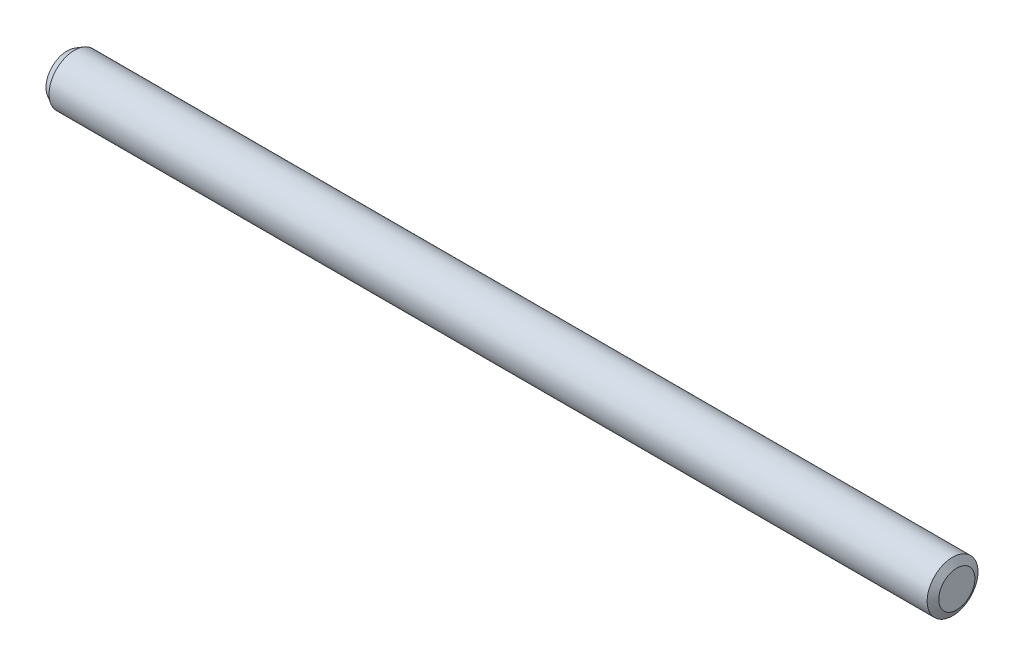
SolidWorks part; units mm, degrees
ref_plane "Front Plane" through (0, 0, 0) normal (0, 0, 1) x (1, 0, 0)
ref_plane "Top Plane" through (0, 0, 0) normal (0, 1, 0) x (1, 0, 0)
ref_plane "Right Plane" through (0, 0, 0) normal (1, 0, 0) x (0, 0, -1)
sketch "Sketch1" plane through (0, 0, 0) normal (1, 0, 0) x (0, 0, -1)
  circle A0 centre (0, 0) radius 3
  dimension "D1" = 6
extrude "Boss-Extrude1" add sketch "Sketch1" along normal mid plane 105
chamfer "Chamfer1" distance 0.5 angle 60 2 edges at (-52.5, 0, -3) (52.5, 0, -3)
